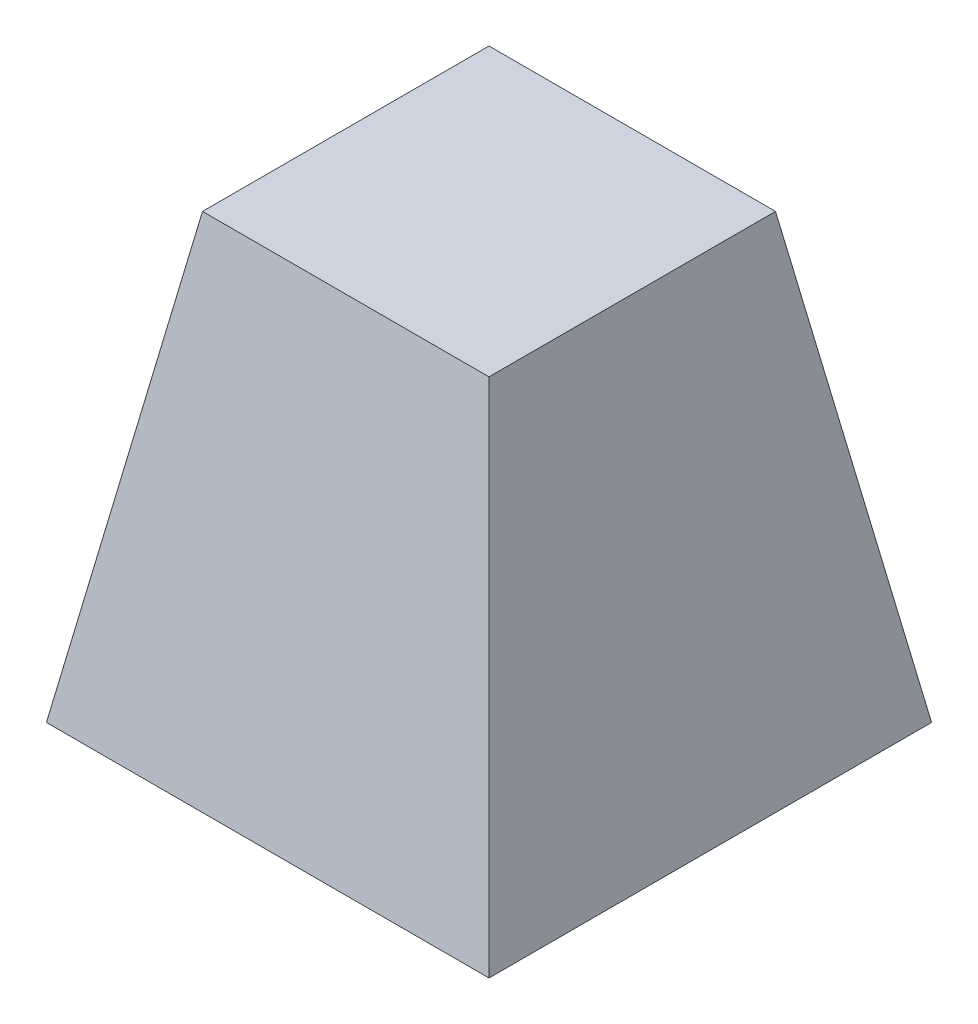
SolidWorks part; units mm, degrees
ref_plane "Front Plane" through (0, 0, 0) normal (0, 0, 1) x (1, 0, 0)
ref_plane "Top Plane" through (0, 0, 0) normal (0, 1, 0) x (1, 0, 0)
ref_plane "Right Plane" through (0, 0, 0) normal (1, 0, 0) x (0, 0, -1)
sketch "Sketch1" plane through (0, 0, 0) normal (0, 1, 0) x (1, 0, 0)
  line L1 (12.7, -12.7) -> (-12.7, -12.7)
  line L2 (12.7, -12.7) -> (12.7, 12.7)
  line L3 (12.7, 12.7) -> (-12.7, 12.7)
  line L4 (-12.7, -12.7) -> (-12.7, 12.7)
  line L5 (12.7, -12.7) -> (-12.7, 12.7) construction
  line L6 (12.7, 12.7) -> (-12.7, -12.7) construction
  point P0 (0, 0)
  dimension "D1" = 25.4
extrude "Boss-Extrude1" add sketch "Sketch1" along normal blind 25.4 draft 10
